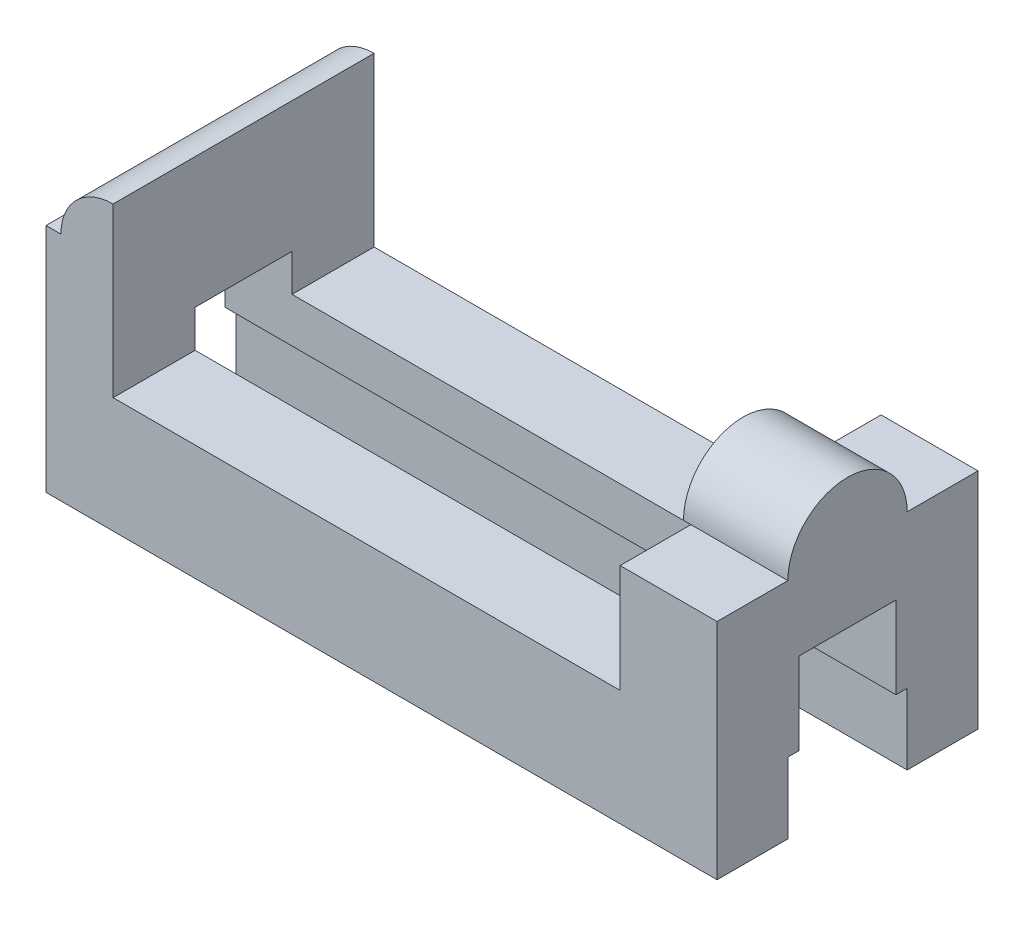
SolidWorks part; units mm, degrees
ref_plane "Front Plane" through (0, 0, 0) normal (0, 0, 1) x (1, 0, 0)
ref_plane "Top Plane" through (0, 0, 0) normal (0, 1, 0) x (1, 0, 0)
ref_plane "Right Plane" through (0, 0, 0) normal (1, 0, 0) x (0, 0, -1)
sketch "Sketch2" plane through (0, 0, 0) normal (0, 0, 1) x (1, 0, 0)
  line L0 (-72, 38) -> (-72, -7)
  line L1 (-90, -38) -> (90, -38)
  line L2 (-90, -38) -> (-90, 38)
  line L3 (-90, 38) -> (-72, 38)
  line L4 (90, -38) -> (90, 38)
  line L5 (-90, -38) -> (90, 38) construction
  line L6 (-90, 38) -> (90, -38) construction
  line L7 (-72, -7) -> (64, -7)
  line L8 (64, -7) -> (64, 38)
  line L10 (64, 38) -> (90, 38)
  point P0 (0, 0)
  dimension "D1" = 180
  dimension "D2" = 76
  dimension "D3" = 45
  dimension "D4" = 26
  dimension "D5" = 18
extrude "Boss-Extrude1" add sketch "Sketch2" along normal mid plane 70 contours L4 L10 L8 L7 L0 L3 L2 L1
sketch "Sketch3" plane through (90, 0, 0) normal (1, 0, 0) x (0, 0, -1)
  line L0 (16, -38) -> (16, -19)
  line L1 (-35, -38) -> (35, -38) construction
  line L2 (16, -19) -> (13, -19)
  line L3 (13, -19) -> (13, 3)
  line L4 (13, 3) -> (-13, 3)
  line L5 (-13, 3) -> (-13, -19)
  line L6 (-13, -19) -> (-16, -19)
  line L7 (-16, -19) -> (-16, -38)
  line L8 (-16, -38) -> (16, -38)
  dimension "D1" = 19
  dimension "D2" = 19
  dimension "D3" = 26
  dimension "D4" = 19
  dimension "D5" = 19
  dimension "D6" = 22
  dimension "D7" = 3
extrude "Cut-Extrude1" cut sketch "Sketch3" against normal through all both and the other way through all
sketch "Sketch5" plane through (0, 0, 35) normal (0, 0, 1) x (1, 0, 0)
  line L0 (-90, 24) -> (-86, 24)
  line L1 (-90, -38) -> (-90, 38) construction
  line L2 (-72, 38) -> (-90, 38)
  line L3 (-90, 38) -> (-90, 24)
  arc A0 (-86, 24) -> (-72, 38) centre (-72, 24) cw
  dimension "D1" = 14
  dimension "D2" = 4
extrude "Cut-Extrude2" cut sketch "Sketch5" against normal blind 70
sketch "Sketch9" plane through (90, 0, 0) normal (1, 0, 0) x (0, 0, -1)
  line L0 (-35, 22) -> (35, 22)
  line L1 (-35, -38) -> (-35, 38) construction
  line L2 (35, -38) -> (35, 38) construction
  line L3 (35, 22) -> (35, 38)
  line L4 (35, 38) -> (-35, 38)
  line L5 (-35, 38) -> (-35, 22)
  dimension "D1" = 16
extrude "Cut-Extrude4" cut sketch "Sketch9" against normal blind 70
sketch "Sketch10" plane through (90, 0, 0) normal (1, 0, 0) x (0, 0, -1)
  line L0 (-35, 22) -> (35, 22) construction
  line L1 (-16, 22) -> (16, 22)
  arc A0 (16, 22) -> (-16, 22) centre (0, 22) ccw
  dimension "D1" = 32
extrude "Boss-Extrude2" add sketch "Sketch10" against normal blind 28
